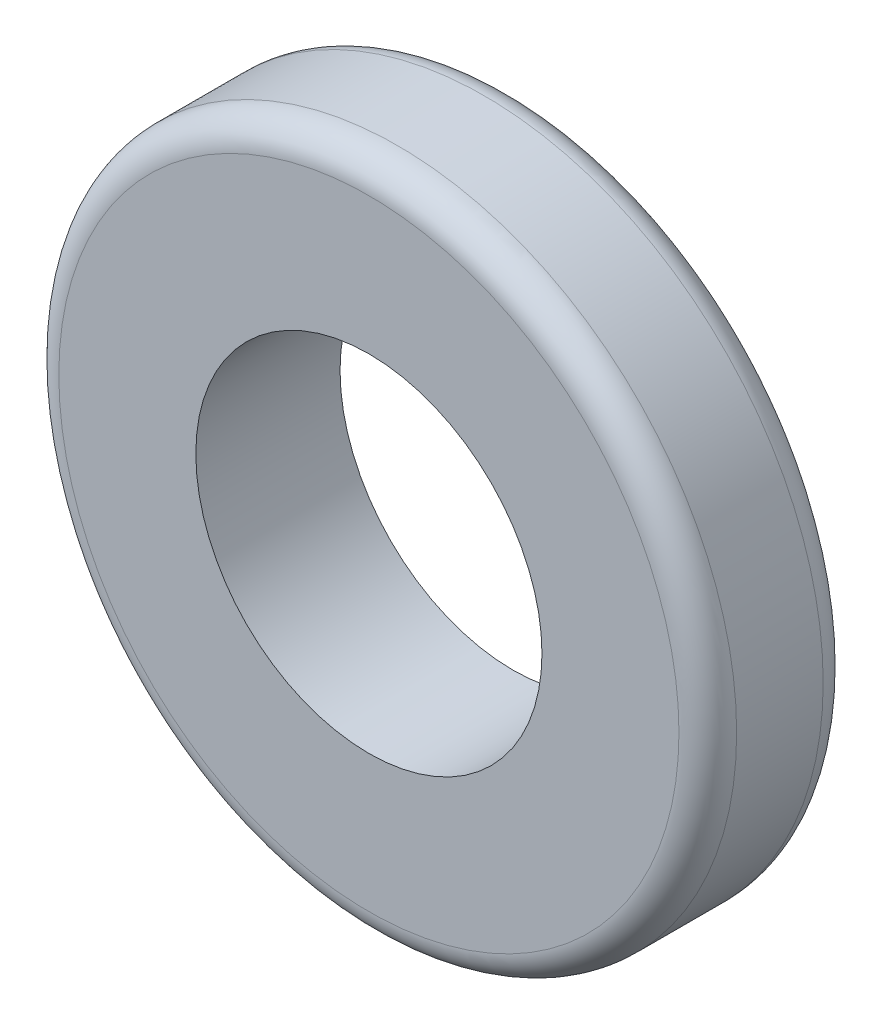
SolidWorks part; units mm, degrees
ref_plane "Front Plane" through (0, 0, 0) normal (0, 0, 1) x (1, 0, 0)
ref_plane "Top Plane" through (0, 0, 0) normal (0, 1, 0) x (1, 0, 0)
ref_plane "Right Plane" through (0, 0, 0) normal (1, 0, 0) x (0, 0, -1)
sketch "Sketch1" plane through (0, 0, 0) normal (0, 0, 1) x (1, 0, 0)
  circle A0 centre (0, 0) radius 23.5
  circle A1 centre (0, 0) radius 12
  dimension "D1" = 24
  dimension "D2" = 47
extrude "Boss-Extrude1" add sketch "Sketch1" along normal blind 10
fillet "Fillet1" radius 2 2 edges at (23.5, 0, 0) (23.5, 0, 10)
